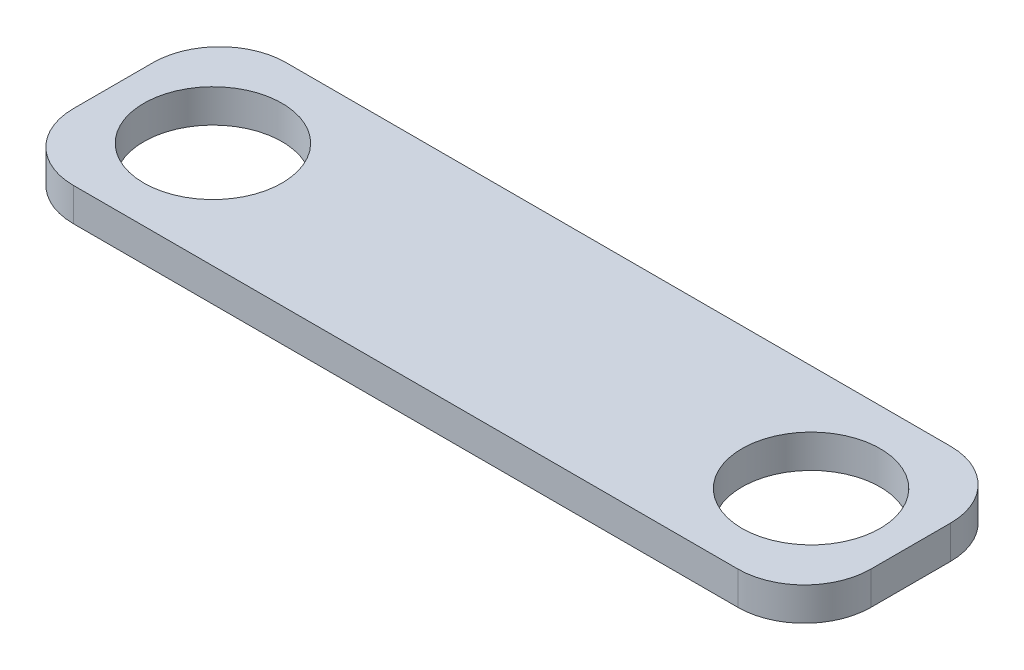
SolidWorks part; units mm, degrees
ref_plane "Front Plane" through (0, 0, 0) normal (0, 0, 1) x (1, 0, 0)
ref_plane "Top Plane" through (0, 0, 0) normal (0, 1, 0) x (1, 0, 0)
ref_plane "Right Plane" through (0, 0, 0) normal (1, 0, 0) x (0, 0, -1)
sketch "Sketch1" plane through (0, 0, 0) normal (0, 1, 0) x (1, 0, 0)
  line L0 (-22.5, 0) -> (22.5, 0) construction
  line L1 (25, -8) -> (-25, -8)
  line L2 (30, -3) -> (30, 3)
  line L3 (25, 8) -> (-25, 8)
  line L4 (-30, -3) -> (-30, 3)
  line L5 (30, -8) -> (-30, 8) construction
  line L6 (30, 8) -> (-30, -8) construction
  circle A0 centre (-22.5, 0) radius 5.2
  circle A1 centre (22.5, 0) radius 5.2
  arc A2 (25, -8) -> (30, -3) centre (25, -3) ccw
  arc A3 (30, 3) -> (25, 8) centre (25, 3) ccw
  arc A4 (-25, -8) -> (-30, -3) centre (-25, -3) cw
  arc A5 (-25, 8) -> (-30, 3) centre (-25, 3) ccw
  point P0 (0, 0)
  point P10 (0, 0)
  dimension "D3" = 10.4
  dimension "D4" = 10.4
  dimension "D6" = 5
  dimension "D1" = 60
  dimension "D2" = 16
  dimension "D5" = 45
extrude "Boss-Extrude1" add sketch "Sketch1" along normal blind 2.5
